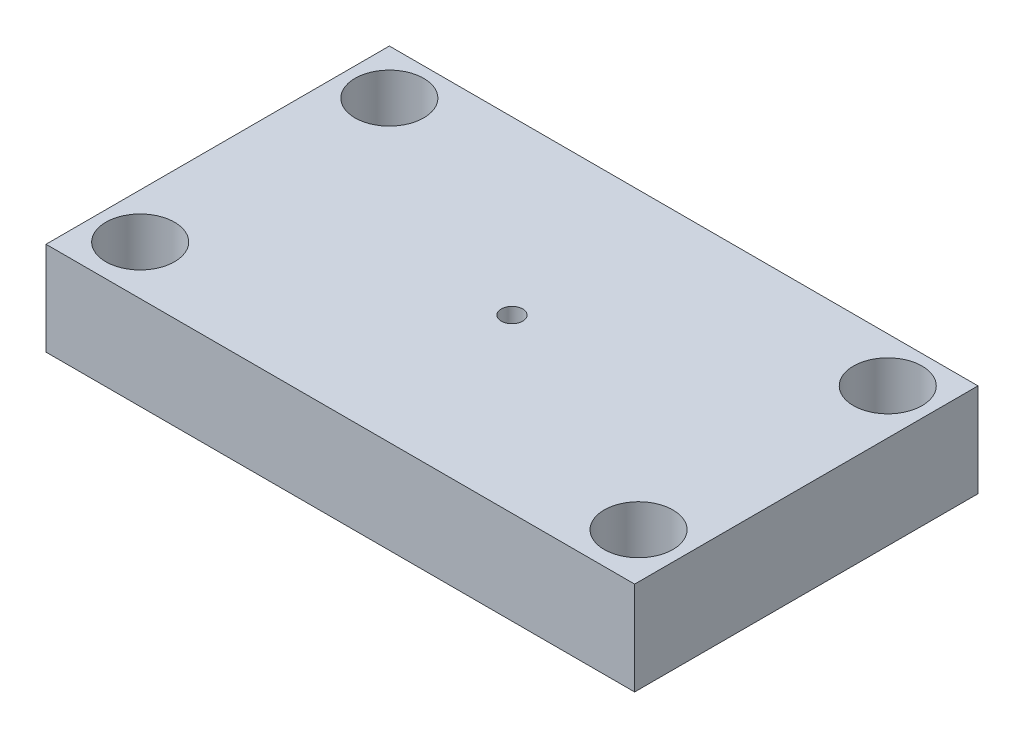
SolidWorks part; units mm, degrees
ref_plane "Front Plane" through (0, 0, 0) normal (0, 0, 1) x (1, 0, 0)
ref_plane "Top Plane" through (0, 0, 0) normal (0, 1, 0) x (1, 0, 0)
ref_plane "Right Plane" through (0, 0, 0) normal (1, 0, 0) x (0, 0, -1)
sketch "Sketch1" plane through (0, 0, 0) normal (0, 1, 0) x (1, 0, 0)
  line L0 (4.6, 30.4) -> (0, 30.4) construction
  line L1 (0, 0) -> (60, 0)
  line L2 (0, 0) -> (0, 35)
  line L3 (0, 35) -> (60, 35)
  line L4 (60, 0) -> (60, 35)
  line L5 (4.6, 30.4) -> (55.4, 30.4) construction
  line L6 (4.6, 30.4) -> (4.6, 5) construction
  line L7 (4.6, 5) -> (55.4, 5) construction
  line L8 (55.4, 30.4) -> (55.4, 5) construction
  line L9 (4.6, 30.4) -> (4.6, 35) construction
  circle A0 centre (4.6, 30.4) radius 3.5
  circle A1 centre (55.4, 30.4) radius 3.5
  circle A2 centre (4.6, 5) radius 3.5
  circle A3 centre (55.4, 5) radius 3.5
  circle A4 centre (30, 17.5) radius 1.0875
  point P13 (30, 30.4)
  point P14 (30, 35)
  point P20 (60, 17.5)
  dimension "D5" = 7
  dimension "D6" = 2.175
  dimension "D1" = 60
  dimension "D2" = 35
  dimension "D3" = 50.8
  dimension "D4" = 25.4
extrude "Boss-Extrude1" add sketch "Sketch1" along normal blind 9.525
